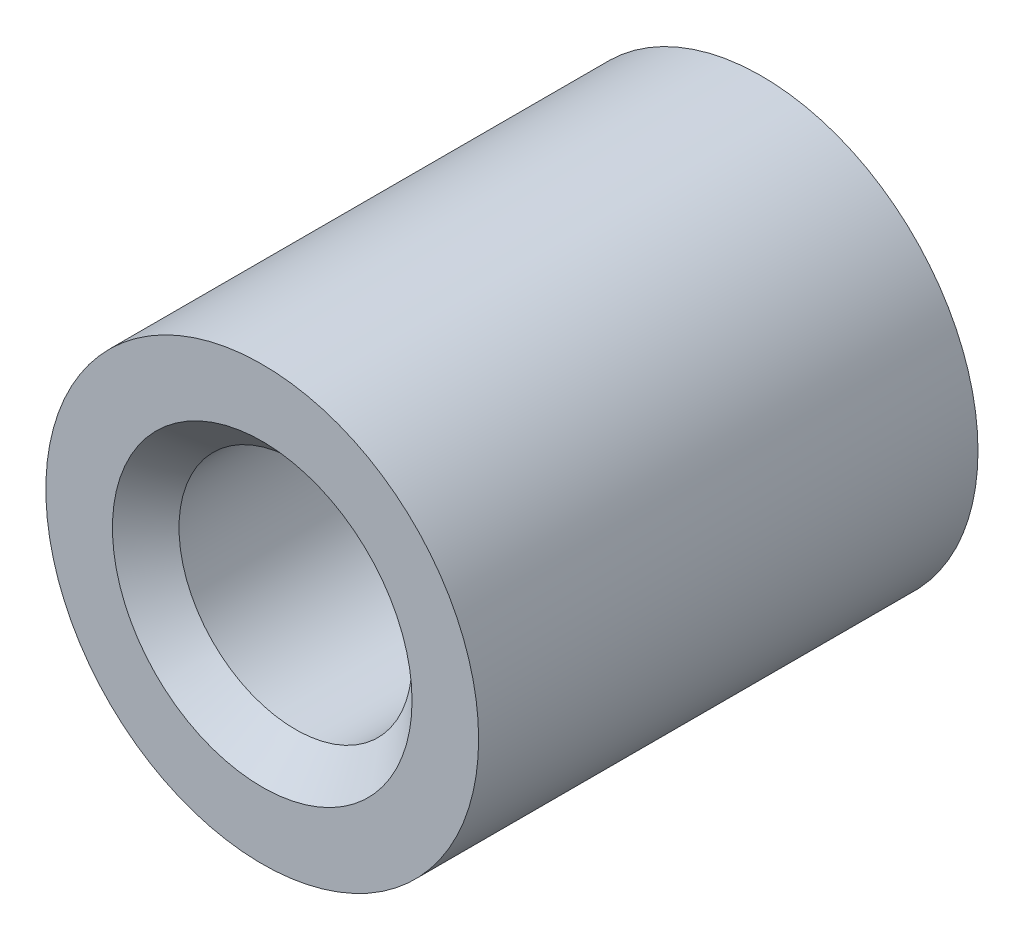
SolidWorks part; units mm, degrees
ref_plane "Front" through (0, 0, 0) normal (0, 0, 1) x (1, 0, 0)
ref_plane "Top" through (0, 0, 0) normal (0, 1, 0) x (1, 0, 0)
ref_plane "Right" through (0, 0, 0) normal (1, 0, 0) x (0, 0, -1)
sketch "Sketch2" plane through (0, 0, 0) normal (0, 0, 1) x (1, 0, 0)
  circle A0 centre (0, 0) radius 3.5
  circle A1 centre (0, 0) radius 6.5
  dimension "D1" = 7
  dimension "D2" = 3
extrude "Boss-Extrude1" add sketch "Sketch2" along normal blind 15
chamfer "Chamfer1" distance 1 angle 45 2 edges at (3.5, 0, 15) (3.5, 0, 0)
